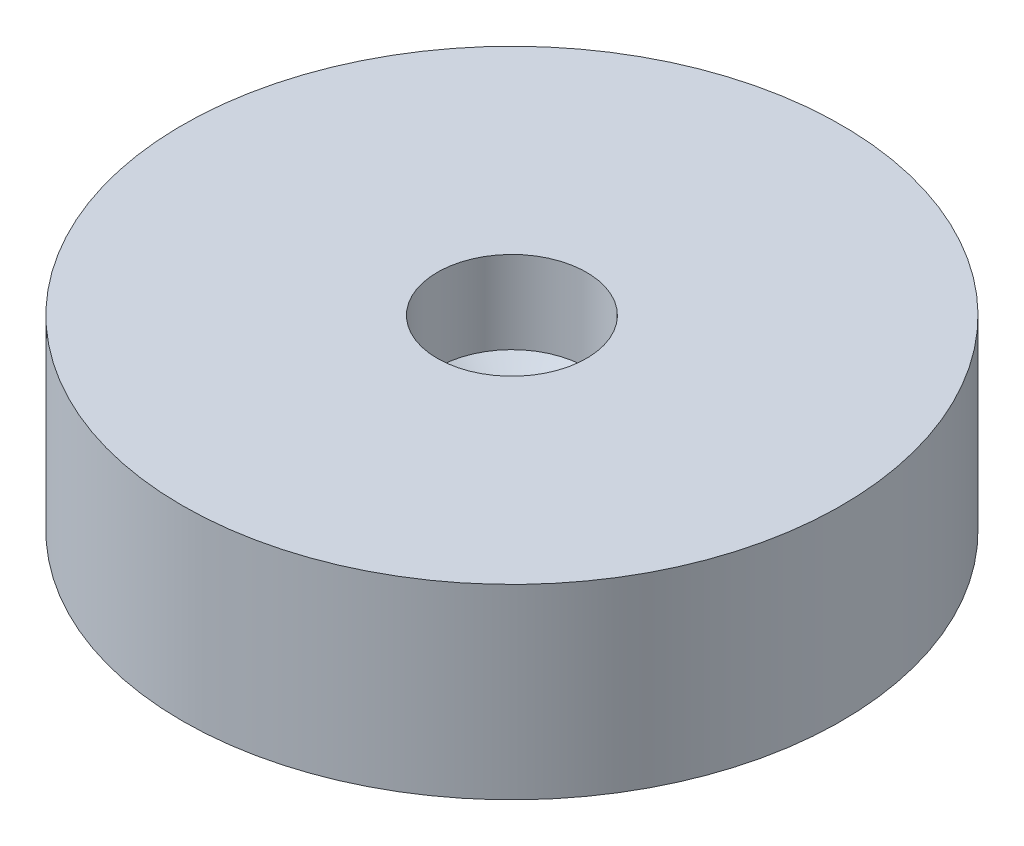
SolidWorks part; units mm, degrees
ref_plane "Front Plane" through (0, 0, 0) normal (0, 0, 1) x (1, 0, 0)
ref_plane "Top Plane" through (0, 0, 0) normal (0, 1, 0) x (1, 0, 0)
ref_plane "Right Plane" through (0, 0, 0) normal (1, 0, 0) x (0, 0, -1)
sketch "Sketch3" plane through (0, 0, 0) normal (0, 0, 1) x (1, 0, 0)
  line L0 (0, 0) -> (22, 0) construction
  line L1 (3.25, 6.4429) -> (6, 8.3684)
  line L2 (22, 0) -> (3.25, 5.4429)
  line L3 (3.25, -13.9932) -> (3.25, 1.2597) construction
  line L4 (0, 0) -> (0, -13.9932) construction
  line L5 (22, 0) -> (26.5, 0)
  line L6 (3.25, 6.4429) -> (3.25, 5.4429)
  line L9 (26.5, 15) -> (26.5, 0)
  line L11 (26.5, 15) -> (6, 15)
  line L12 (3.25, 5.4429) -> (3.25, 6.4429) construction
  line L13 (6, 8.3684) -> (6, 15)
  dimension "D1" = 22
  dimension "D2" = 1
  dimension "D3" = 3.25
  dimension "D4" = 4.5
  dimension "D6" = 6
  dimension "15" = 15
  dimension "D5" = 5.4429
  dimension "D7" = 145
revolve "Revolve1" add sketch "Sketch3" angle 360 about L4
